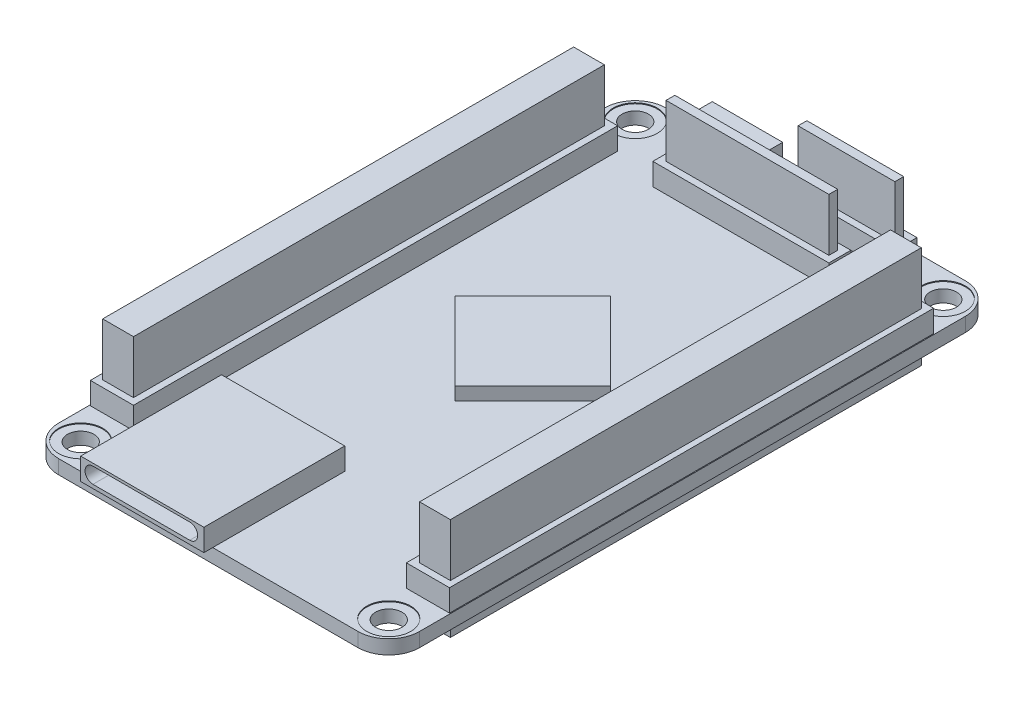
SolidWorks part; units mm, degrees
ref_plane "Спереди" through (0, 0, 0) normal (0, 0, 1) x (1, 0, 0)
ref_plane "Сверху" through (0, 0, 0) normal (0, 1, 0) x (1, 0, 0)
ref_plane "Справа" through (0, 0, 0) normal (1, 0, 0) x (0, 0, -1)
sketch "Эскиз1" plane through (0, 0, 0) normal (0, 1, 0) x (1, 0, 0)
  line L1 (-13.6875, 32.0562) -> (27.3125, 32.0562)
  line L2 (-13.6875, 32.0562) -> (-13.6875, -36.9438)
  line L3 (-13.6875, -36.9438) -> (27.3125, -36.9438)
  line L4 (27.3125, 32.0562) -> (27.3125, -36.9438)
  dimension "D1" = 69
  dimension "D2" = 41
extrude "Бобышка-Вытянуть1" add sketch "Эскиз1" along normal blind 1.6
sketch "Эскиз3" plane through (0, 1.6, 0) normal (0, 1, 0) x (1, 0, 0)
  circle A0 centre (-10.6875, 29.0563) radius 2.5
  circle A1 centre (24.3125, 29.0563) radius 2.5
  circle A2 centre (-10.6875, -33.9438) radius 2.5
  circle A3 centre (24.3125, -33.9438) radius 2.5
extrude "Вырез-Вытянуть1" cut sketch "Эскиз3" against normal blind 0.1
fillet "Скругление4" radius 3.5 4 edges at (-13.6875, 0.8, -32.0562) (27.3125, 0.8, -32.0562) (27.3125, 0.8, 36.9438) (-13.6875, 0.8, 36.9438)
sketch "Эскиз4" plane through (0, 1.5, 0) normal (0, 1, 0) x (1, 0, 0)
  circle A0 centre (-10.6875, 29.0563) radius 1.5
  circle A3 centre (24.3125, 29.0563) radius 1.5
  circle A6 centre (-10.6875, -33.9438) radius 1.5
  circle A8 centre (24.3125, -33.9438) radius 1.5
extrude "Вырез-Вытянуть2" cut sketch "Эскиз4" against normal blind 1.9
sketch "Эскиз5" plane through (0, 1.6, 0) normal (0, 1, 0) x (1, 0, 0)
  line L1 (-13.5875, 25.0563) -> (-8.6875, 25.0563)
  line L2 (-13.5875, 25.0563) -> (-13.5875, -29.9438)
  line L3 (-13.5875, -29.9438) -> (-8.6875, -29.9437)
  line L4 (-8.6875, 25.0563) -> (-8.6875, -29.9437)
  dimension "D1" = 55
  dimension "D2" = 4.9
extrude "Бобышка-Вытянуть2" add sketch "Эскиз5" along normal blind 2.5
sketch "Эскиз6" plane through (0, 1.6, 0) normal (0, 1, 0) x (1, 0, 0)
  line L1 (22.3125, 25.0563) -> (27.2125, 25.0563)
  line L2 (22.3125, 25.0563) -> (22.3125, -29.9437)
  line L3 (22.3125, -29.9437) -> (27.2125, -29.9437)
  line L4 (27.2125, 25.0563) -> (27.2125, -29.9437)
  dimension "D1" = 4.9
  dimension "D2" = 55
extrude "Бобышка-Вытянуть3" add sketch "Эскиз6" along normal blind 2.5
sketch "Эскиз7" plane through (0, 1.6, 0) normal (0, 1, 0) x (1, 0, 0)
  line L1 (-3.1875, 26.0563) -> (16.8125, 26.0563)
  line L2 (-3.1875, 26.0563) -> (-3.1875, 23.5563)
  line L3 (-3.1875, 23.5563) -> (16.8125, 23.5563)
  line L4 (16.8125, 26.0563) -> (16.8125, 23.5563)
  dimension "D1" = 2.5
  dimension "D2" = 20
extrude "Бобышка-Вытянуть4" add sketch "Эскиз7" along normal blind 2.5
sketch "Эскиз8" plane through (0, 1.6, 0) normal (0, 1, 0) x (1, 0, 0)
  line L1 (6.8125, 31.0563) -> (19.3125, 31.0563)
  line L2 (6.8125, 31.0563) -> (6.8125, 28.5562)
  line L3 (6.8125, 28.5562) -> (19.3125, 28.5562)
  line L4 (19.3125, 31.0563) -> (19.3125, 28.5562)
  dimension "D1" = 2.5
  dimension "D2" = 12.5
extrude "Бобышка-Вытянуть5" add sketch "Эскиз8" along normal blind 2.5
sketch "Эскиз9" plane through (0, 1.6, 0) normal (0, 1, 0) x (1, 0, 0)
  line L1 (-5.6875, 32.8062) -> (2.3125, 32.8062)
  line L2 (-5.6875, 32.8062) -> (-5.6875, 27.8063)
  line L3 (-5.6875, 27.8063) -> (2.3125, 27.8063)
  line L4 (2.3125, 32.8062) -> (2.3125, 27.8063)
  dimension "D1" = 8
  dimension "D2" = 5
extrude "Бобышка-Вытянуть6" add sketch "Эскиз9" along normal blind 2.5
sketch "Эскиз10" plane through (0, 0, -32.8062) normal (0, 0, -1) x (-1, 0, 0)
  line L0 (-0.7151, 2.7535) -> (4.1884, 2.7535) construction
  line L1 (-0.7151, 3.3931) -> (4.1884, 3.3931)
  line L2 (-0.7151, 2.114) -> (4.1884, 2.114)
  arc A0 (-0.7151, 3.3931) -> (-0.7151, 2.114) centre (-0.7151, 2.7535) ccw
  arc A1 (4.1884, 2.114) -> (4.1884, 3.3931) centre (4.1884, 2.7535) ccw
  point P2 (1.7366, 2.7535)
extrude "Вырез-Вытянуть3" cut sketch "Эскиз10" against normal blind 4
sketch "Эскиз11" plane through (0, 1.6, 0) normal (0, 1, 0) x (1, 0, 0)
  line L1 (-2.1875, 0.0563) -> (6.6513, 8.8951)
  line L2 (-2.1875, 0.0563) -> (6.6513, -8.7826)
  line L3 (6.6513, -8.7826) -> (15.4902, 0.0563)
  line L4 (6.6513, 8.8951) -> (15.4902, 0.0563)
  dimension "D1" = 12.5
  dimension "D2" = 12.5
extrude "Бобышка-Вытянуть7" add sketch "Эскиз11" along normal blind 1.5
sketch "Эскиз12" plane through (0, 4.1, 0) normal (0, 1, 0) x (1, 0, 0)
  line L1 (-12.9375, 24.3063) -> (-9.4375, 24.3063)
  line L2 (-12.9375, 24.3063) -> (-12.9375, -29.1937)
  line L3 (-12.9375, -29.1937) -> (-9.4375, -29.1937)
  line L4 (-9.4375, 24.3063) -> (-9.4375, -29.1937)
  dimension "D1" = 3.5
  dimension "D2" = 53.5
extrude "Бобышка-Вытянуть8" add sketch "Эскиз12" along normal blind 6
sketch "Эскиз13" plane through (0, 4.1, 0) normal (0, 1, 0) x (1, 0, 0)
  line L1 (23.0625, 24.3063) -> (26.5625, 24.3063)
  line L2 (23.0625, 24.3063) -> (23.0625, -29.1937)
  line L3 (23.0625, -29.1937) -> (26.5625, -29.1937)
  line L4 (26.5625, 24.3063) -> (26.5625, -29.1937)
  dimension "D1" = 3.5
  dimension "D2" = 53.5
extrude "Бобышка-Вытянуть9" add sketch "Эскиз13" along normal blind 6
sketch "Эскиз14" plane through (0, 4.1, 0) normal (0, 1, 0) x (1, 0, 0)
  line L1 (-2.4375, 25.3063) -> (16.0625, 25.3063)
  line L2 (-2.4375, 25.3063) -> (-2.4375, 24.3063)
  line L3 (-2.4375, 24.3063) -> (16.0625, 24.3063)
  line L4 (16.0625, 25.3063) -> (16.0625, 24.3063)
  dimension "D1" = 1
  dimension "D2" = 18.5
extrude "Бобышка-Вытянуть10" add sketch "Эскиз14" along normal blind 6
sketch "Эскиз15" plane through (0, 4.1, 0) normal (0, 1, 0) x (1, 0, 0)
  line L1 (7.5625, 30.3062) -> (18.5625, 30.3062)
  line L2 (7.5625, 30.3062) -> (7.5625, 29.3062)
  line L3 (7.5625, 29.3062) -> (18.5625, 29.3062)
  line L4 (18.5625, 30.3062) -> (18.5625, 29.3062)
  dimension "D1" = 1
  dimension "D2" = 11
extrude "Бобышка-Вытянуть11" add sketch "Эскиз15" along normal blind 6
sketch "Эскиз16" plane through (0, 0, 0) normal (0, -1, 0) x (-1, 0, 0)
  line L1 (12.9375, -29.1937) -> (9.4375, -29.1937)
  line L2 (12.9375, -29.1937) -> (12.9375, 24.3063)
  line L3 (12.9375, 24.3063) -> (9.4375, 24.3063)
  line L4 (9.4375, -29.1937) -> (9.4375, 24.3063)
  line L5 (-23.0625, -29.1937) -> (-26.5625, -29.1937)
  line L6 (-23.0625, -29.1937) -> (-23.0625, 24.3063)
  line L7 (-23.0625, 24.3063) -> (-26.5625, 24.3063)
  line L8 (-26.5625, -29.1937) -> (-26.5625, 24.3063)
  line L9 (2.4375, 24.3063) -> (-16.0625, 24.3063)
  line L10 (2.4375, 24.3063) -> (2.4375, 25.3063)
  line L11 (2.4375, 25.3063) -> (-16.0625, 25.3063)
  line L12 (-16.0625, 24.3063) -> (-16.0625, 25.3063)
  line L13 (-7.5625, 29.3062) -> (-18.5625, 29.3062)
  line L14 (-7.5625, 29.3062) -> (-7.5625, 30.3062)
  line L15 (-7.5625, 30.3062) -> (-18.5625, 30.3062)
  line L16 (-18.5625, 29.3062) -> (-18.5625, 30.3062)
extrude "Бобышка-Вытянуть12" add sketch "Эскиз16" along normal blind 1.5
sketch "Эскиз17" plane through (0, 0, 0) normal (0, -1, 0) x (-1, 0, 0)
  circle A0 centre (10.6875, -33.9438) radius 2.5
  circle A1 centre (-24.3125, -33.9438) radius 2.5
  circle A2 centre (10.6875, 29.0563) radius 2.5
  circle A3 centre (-24.3125, 29.0563) radius 2.5
extrude "Вырез-Вытянуть4" cut sketch "Эскиз17" against normal blind 0.1
sketch "Эскиз18" plane through (0, 1.6, 0) normal (0, 1, 0) x (1, 0, 0)
  line L1 (-6.6875, -21.9438) -> (7.3125, -21.9438)
  line L2 (-6.6875, -21.9438) -> (-6.6875, -37.9438)
  line L3 (-6.6875, -37.9438) -> (7.3125, -37.9438)
  line L4 (7.3125, -21.9438) -> (7.3125, -37.9438)
  dimension "D1" = 14
  dimension "D2" = 16
extrude "Бобышка-Вытянуть13" add sketch "Эскиз18" along normal blind 2.5
sketch "Эскиз19" plane through (0, 0, 37.9438) normal (0, 0, 1) x (1, 0, 0)
  line L0 (-5.297, 2.9142) -> (5.7039, 2.9142) construction
  line L1 (-5.297, 3.8097) -> (5.7039, 3.8097)
  line L2 (-5.297, 2.0188) -> (5.7039, 2.0188)
  arc A0 (-5.297, 3.8097) -> (-5.297, 2.0188) centre (-5.297, 2.9142) ccw
  arc A1 (5.7039, 2.0188) -> (5.7039, 3.8097) centre (5.7039, 2.9142) ccw
  point P2 (0.2034, 2.9142)
extrude "Вырез-Вытянуть5" cut sketch "Эскиз19" against normal blind 15
